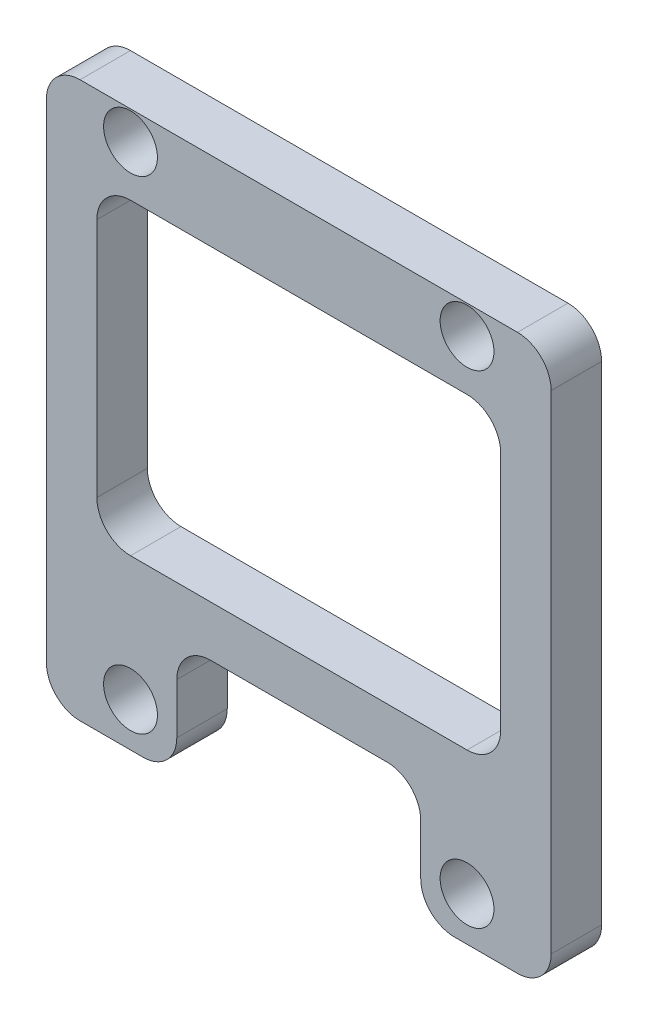
SolidWorks part; units mm, degrees
ref_plane "前视基准面" through (0, 0, 0) normal (0, 0, 1) x (1, 0, 0)
ref_plane "上视基准面" through (0, 0, 0) normal (0, 1, 0) x (1, 0, 0)
ref_plane "右视基准面" through (0, 0, 0) normal (1, 0, 0) x (0, 0, -1)
sketch "草图1" plane through (0, 0, 0) normal (0, 0, 1) x (1, 0, 0)
  line L0 (15, 35) -> (15, -49965) construction
  line L1 (0, 0) -> (30, 0)
  line L2 (0, 0) -> (0, 33)
  line L3 (0, 33) -> (30, 33)
  line L4 (30, 0) -> (30, 33)
  line L5 (5, 31.3) -> (25, 31.3) construction
  line L6 (5, 31.3) -> (5, 2.6) construction
  line L7 (5, 2.6) -> (25, 2.6) construction
  line L8 (25, 31.3) -> (25, 2.6) construction
  circle A0 centre (5, 31.3) radius 1.6
  circle A1 centre (25, 31.3) radius 1.6
  circle A2 centre (25, 2.6) radius 1.6
  circle A3 centre (5, 2.6) radius 1.6
  point P11 (15, 33)
  point P12 (15, 0)
  point P17 (15, 31.3)
  dimension "D6" = 3.2
  dimension "D5" = 1.7
  dimension "D1" = 30
  dimension "D2" = 33
  dimension "D3" = 20
  dimension "D4" = 28.7
extrude "凸台-拉伸1" add sketch "草图1" along normal blind 3
sketch "草图2" plane through (0, 0, 3) normal (0, 0, 1) x (1, 0, 0)
  line L0 (0, 0) -> (30, 0) construction
  line L5 (7.75, 0) -> (22.25, 0)
  line L6 (7.75, 0) -> (7.75, 7)
  line L7 (7.75, 7) -> (22.25, 7)
  line L8 (22.25, 0) -> (22.25, 7)
  line L9 (15, 35) -> (15, -49965) construction
  line L10 (30, 33) -> (0, 33) construction
  line L16 (0, 33) -> (0, 0) construction
  line L17 (27, 10) -> (3, 10)
  line L18 (27, 10) -> (27, 28.3)
  line L19 (27, 28.3) -> (3, 28.3)
  line L20 (3, 10) -> (3, 28.3)
  line L21 (27, 10) -> (3, 28.3) construction
  line L22 (27, 28.3) -> (3, 10) construction
  circle A1 centre (5, 31.3) radius 1.6 construction
  point P10 (15, 33)
  point P11 (15, 7)
  point P12 (15, 19.15)
  dimension "D3" = 3
  dimension "D1" = 14.5
  dimension "D2" = 7
  dimension "D4" = 3
  dimension "D5" = 3
extrude "切除-拉伸1" cut sketch "草图2" against normal through all
fillet "圆角1" radius 2 4 edges at (0, 33, 1.5) (30, 33, 1.5) (30, 0, 1.5) (0, 0, 1.5)
fillet "圆角2" radius 2 8 edges at (3, 28.3, 1.5) (27, 28.3, 1.5) (27, 10, 1.5) (7.75, 0, 1.5) (7.75, 7, 1.5) (22.25, 7, 1.5) (22.25, 0, 1.5) (3, 10, 1.5)
